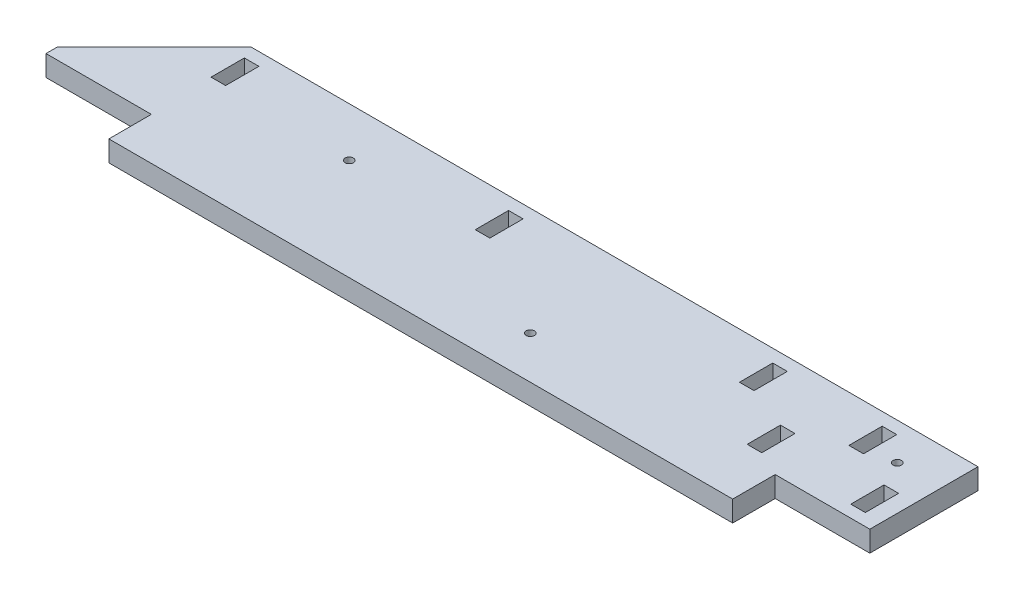
SolidWorks part; units mm, degrees
ref_plane "Front Plane" through (0, 0, 0) normal (0, 0, 1) x (1, 0, 0)
ref_plane "Top Plane" through (0, 0, 0) normal (0, 1, 0) x (1, 0, 0)
ref_plane "Right Plane" through (0, 0, 0) normal (1, 0, 0) x (0, 0, -1)
sketch "Sketch1" plane through (0, 0, 0) normal (0, 1, 0) x (1, 0, 0)
  line L1 (-125.73, -16.51) -> (125.73, -16.51)
  line L2 (-125.73, -16.51) -> (-125.73, 16.51)
  line L3 (-125.73, 16.51) -> (125.73, 16.51)
  line L4 (125.73, -16.51) -> (125.73, 16.51)
  line L5 (-125.73, -16.51) -> (125.73, 16.51) construction
  line L6 (-125.73, 16.51) -> (125.73, -16.51) construction
  point P0 (0, 0)
  dimension "D1" = 33.02
  dimension "D2" = 251.46
extrude "Boss-Extrude1" add sketch "Sketch1" along normal mid plane 6.35
sketch "Sketch2" plane through (0, -3.175, 0) normal (0, -1, 0) x (1, 0, 0)
  line L0 (-58.7746, -54.0014) -> (-125.73, 12.954) construction
  line L1 (-96.266, -16.51) -> (-125.73, 12.954)
  line L2 (-125.73, 12.954) -> (-125.73, -16.51)
  line L3 (-125.73, -16.51) -> (-96.266, -16.51)
  line L4 (125.73, -16.51) -> (-125.73, -16.51) construction
extrude "Cut-Extrude1" cut sketch "Sketch2" against normal through all
sketch "Sketch3" plane through (0, 3.175, 0) normal (0, 1, 0) x (1, 0, 0)
  line L0 (125.73, -16.51) -> (100.2074, -16.51) construction
  line L1 (-125.73, -16.51) -> (125.73, -16.51) construction
  line L2 (100.2074, -16.51) -> (100.2074, 16.51) construction
  line L3 (125.73, 16.51) -> (-96.266, 16.51) construction
  line L4 (-96.266, 16.51) -> (-96.266, -16.51) construction
  line L6 (96.8397, -16.51) -> (-93.5729, -16.51)
  line L7 (96.8397, -16.51) -> (96.8397, -29.477)
  line L8 (96.8397, -29.477) -> (-93.5729, -29.477)
  line L9 (-93.5729, -16.51) -> (-93.5729, -29.477)
extrude "Boss-Extrude2" add sketch "Sketch3" against normal up to surface (6.35 mm away) up to face at (-19.2532, -3.175, 2.5908)
sketch "Sketch5" plane through (0, 3.175, 0) normal (0, 1, 0) x (1, 0, 0)
  line L0 (125.73, -16.51) -> (125.73, 16.51) construction
  line L2 (125.73, 16.51) -> (-96.266, 16.51) construction
  line L3 (125.73, -16.51) -> (125.73, 16.51) construction
  line L4 (-125.73, -12.954) -> (-125.73, -16.51) construction
  circle A0 centre (112.3696, 5.2324) radius 1.2573
  circle A1 centre (22.098, -16.51) radius 1.2573
  circle A2 centre (-51.2064, 1.524) radius 1.2573
  point P12 (125.73, 0)
  dimension "D1" = 13.3604
  dimension "D5" = 2.5146
  dimension "D6" = 2.5146
  dimension "D9" = 2.5146
  dimension "D2" = 11.2776
  dimension "D3" = 33.02
  dimension "D4" = 103.632
  dimension "D7" = 14.986
  dimension "D8" = 74.5236
extrude "Cut-Extrude2" cut sketch "Sketch5" against normal through all
sketch "Sketch6" plane through (0, -3.175, 0) normal (0, -1, 0) x (1, 0, 0)
  line L0 (84.582, 12.801) -> (89.027, 12.801) construction
  line L1 (89.027, 12.801) -> (89.027, 2.641) construction
  line L2 (84.582, 12.801) -> (84.582, 2.641) construction
  line L3 (84.582, 2.641) -> (89.027, 2.641) construction
  line L4 (116.205, 12.801) -> (120.65, 12.801) construction
  line L5 (116.205, 12.801) -> (116.205, 2.641) construction
  line L6 (116.205, 2.641) -> (120.65, 2.641) construction
  line L7 (120.65, 12.801) -> (120.65, 2.641) construction
  line L8 (100.3935, -2.439) -> (104.8385, -2.439) construction
  line L27 (104.8385, -2.439) -> (104.8385, -12.599) construction
  line L28 (100.3935, -2.439) -> (100.3935, -12.599) construction
  line L29 (100.3935, -12.599) -> (104.8385, -12.599) construction
  line L30 (66.9925, -2.439) -> (66.9925, -12.599) construction
  line L31 (66.9925, -2.439) -> (71.4375, -2.439) construction
  line L32 (71.4375, -2.439) -> (71.4375, -12.599) construction
  line L33 (66.9925, -12.599) -> (71.4375, -12.599) construction
  line L34 (-13.6525, -12.599) -> (-13.6525, -2.439) construction
  line L35 (-9.2075, -12.599) -> (-9.2075, -2.439) construction
  line L36 (-94.2975, -2.439) -> (-89.8525, -2.439) construction
  line L37 (-94.2975, -12.599) -> (-89.8525, -12.599) construction
  line L38 (-89.8525, -2.439) -> (-89.8525, -12.599) construction
  line L39 (-94.2975, -2.439) -> (-94.2975, -12.599) construction
  line L40 (-9.2075, -2.439) -> (-13.6525, -2.439) construction
  line L41 (-9.2075, -12.599) -> (-13.6525, -12.599) construction
  line L42 (84.582, 12.801) -> (89.027, 12.801)
  line L43 (89.027, 12.801) -> (89.027, 2.641)
  line L44 (84.582, 12.801) -> (84.582, 2.641)
  line L45 (84.582, 2.641) -> (89.027, 2.641)
  line L46 (116.205, 12.801) -> (120.65, 12.801)
  line L47 (116.205, 12.801) -> (116.205, 2.641)
  line L48 (116.205, 2.641) -> (120.65, 2.641)
  line L49 (120.65, 12.801) -> (120.65, 2.641)
  line L50 (100.3935, -2.439) -> (104.8385, -2.439)
  line L51 (104.8385, -2.439) -> (104.8385, -12.599)
  line L52 (100.3935, -2.439) -> (100.3935, -12.599)
  line L53 (100.3935, -12.599) -> (104.8385, -12.599)
  line L54 (66.9925, -2.439) -> (66.9925, -12.599)
  line L55 (66.9925, -2.439) -> (71.4375, -2.439)
  line L56 (71.4375, -2.439) -> (71.4375, -12.599)
  line L57 (66.9925, -12.599) -> (71.4375, -12.599)
  line L58 (-13.6525, -12.599) -> (-13.6525, -2.439)
  line L59 (-9.2075, -12.599) -> (-9.2075, -2.439)
  line L60 (-94.2975, -2.439) -> (-89.8525, -2.439)
  line L61 (-94.2975, -12.599) -> (-89.8525, -12.599)
  line L62 (-89.8525, -2.439) -> (-89.8525, -12.599)
  line L63 (-94.2975, -2.439) -> (-94.2975, -12.599)
  line L64 (-9.2075, -2.439) -> (-13.6525, -2.439)
  line L65 (-9.2075, -12.599) -> (-13.6525, -12.599)
extrude "Cut-Extrude4" cut sketch "Sketch6" against normal through all
equation "\"D1@Boss-Extrude1\"=\"GMaterial@Platform.assembly\""
